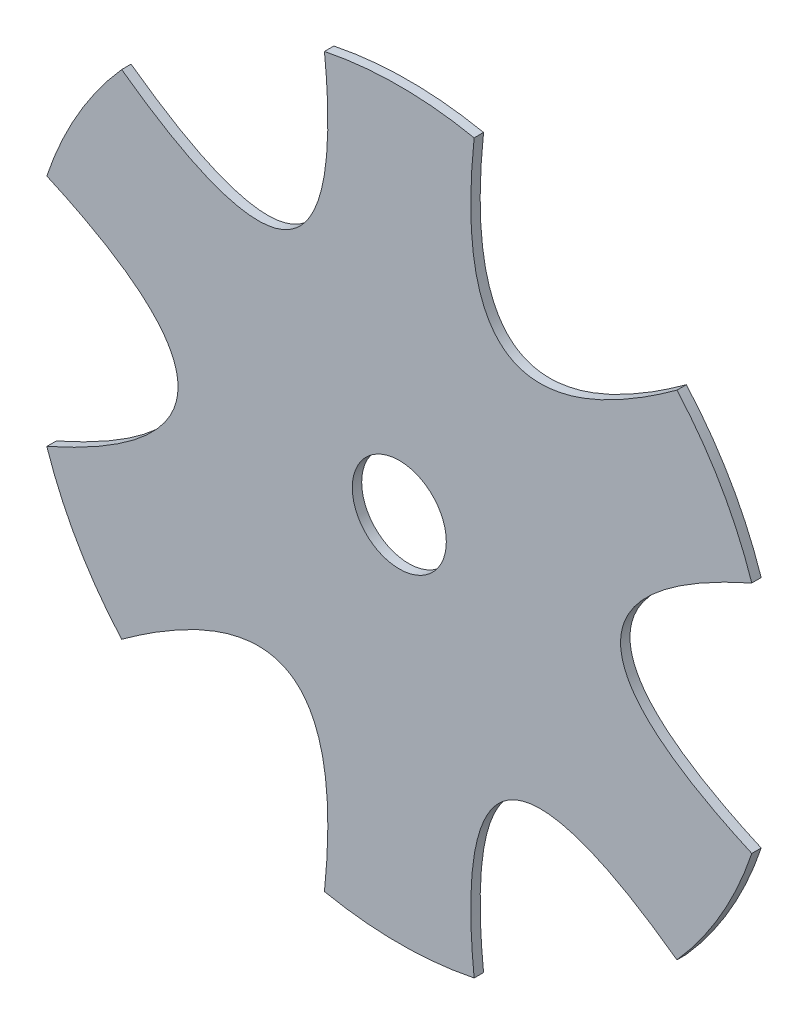
SolidWorks part; units mm, degrees
material "Plain Carbon Steel"
ref_plane "Front Plane" through (0, 0, 0) normal (0, 0, 1) x (1, 0, 0)
ref_plane "Top Plane" through (0, 0, 0) normal (0, 1, 0) x (1, 0, 0)
ref_plane "Right Plane" through (0, 0, 0) normal (1, 0, 0) x (0, 0, -1)
sketch "Sketch1" plane through (0, 0, 0) normal (0, 0, 1) x (1, 0, 0)
  circle A0 centre (0, 0) radius 125.4125
  dimension "D1" = 250.825
extrude "Boss-Extrude1" add sketch "Sketch1" along normal blind 3.175
sketch "Sketch2" plane through (0, 0, 3.175) normal (0, 0, 1) x (1, 0, 0)
  arc A0 (93.7481, 83.3041) -> (25.2694, 122.8403) centre (0, 0) ccw
  spline S0 degree 2 poles (93.7481, 83.3041) (15.2066, 26.3386) (25.2694, 122.8403) knots 0 0 0 1 1 1
extrude "Cut-Extrude1" cut sketch "Sketch2" against normal through all
pattern_circular "CirPattern1" count 6 over 360 about axis through (0, 0, 3.175) along (0, 0, -1) of "Cut-Extrude1"
sketch "Sketch3" plane through (0, 0, 0) normal (0, 0, -1) x (-1, 0, 0)
  circle A0 centre (0, 0) radius 15.875
  dimension "D1" = 31.75
extrude "Cut-Extrude2" cut sketch "Sketch3" against normal blind 50.8 contours A0
